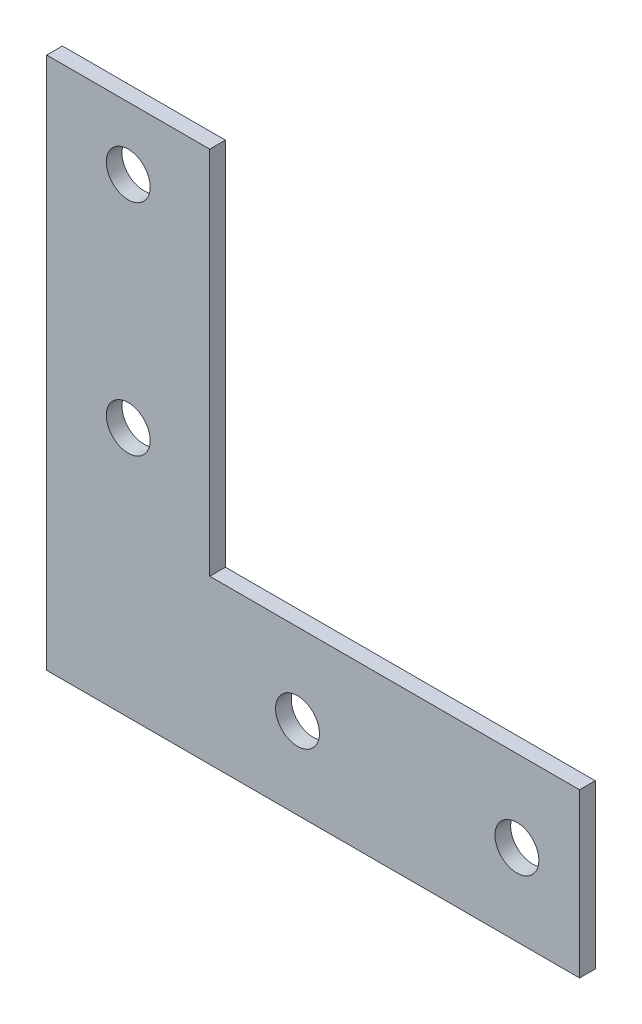
SolidWorks part; units mm, degrees
ref_plane "Спереди" through (0, 0, 0) normal (0, 0, 1) x (1, 0, 0)
ref_plane "Сверху" through (0, 0, 0) normal (0, 1, 0) x (1, 0, 0)
ref_plane "Справа" through (0, 0, 0) normal (1, 0, 0) x (0, 0, -1)
sketch "Эскиз1" plane through (0, 0, 0) normal (0, 0, 1) x (1, 0, 0)
  line L5 (0, 85) -> (0, 0)
  line L6 (0, 0) -> (85, 0)
  line L11 (85, 0) -> (85, 26)
  line L12 (85, 26) -> (26, 26)
  line L16 (26, 26) -> (26, 85)
  line L17 (26, 85) -> (0, 85)
  line L18 (85, 13) -> (75, 13) construction
  line L19 (75, 13) -> (40, 13) construction
  line L20 (13, 85) -> (13, 75) construction
  line L21 (13, 75) -> (13, 40) construction
  circle A6 centre (13, 75) radius 3.5
  circle A7 centre (13, 40) radius 3.5
  circle A8 centre (40, 13) radius 3.5
  circle A9 centre (75, 13) radius 3.5
  dimension "D4" = 10
  dimension "D5" = 35
  dimension "D3" = 7
  dimension "D1" = 85
  dimension "D2" = 26
extrude "Бобышка-Вытянуть1" add sketch "Эскиз1" along normal blind 2.5
